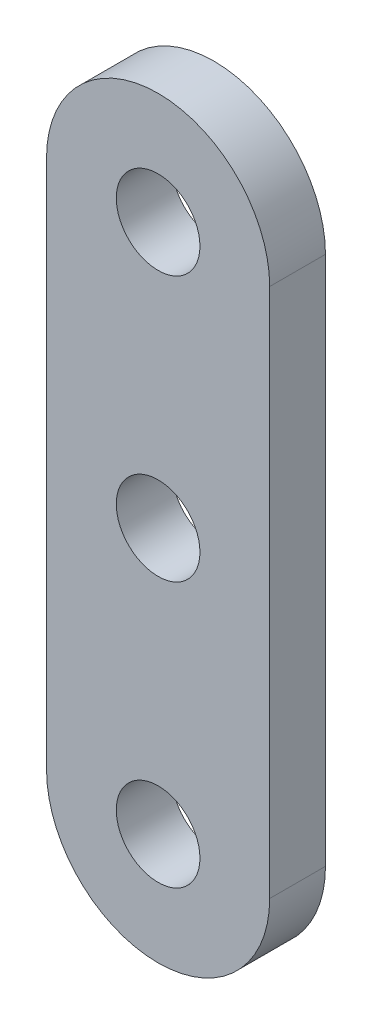
SolidWorks part; units mm, degrees
ref_plane "Front Plane" through (0, 0, 0) normal (0, 0, 1) x (1, 0, 0)
ref_plane "Top Plane" through (0, 0, 0) normal (0, 1, 0) x (1, 0, 0)
ref_plane "Right Plane" through (0, 0, 0) normal (1, 0, 0) x (0, 0, -1)
sketch "Sketch1" plane through (0, 0, 0) normal (0, 0, 1) x (1, 0, 0)
  line L0 (0, 27.7812) -> (0, 2.3813)
  line L1 (0, 0) -> (0, 30.1625) construction
  line L2 (-6.35, 0) -> (-6.35, 30.1625)
  line L3 (6.35, 0) -> (6.35, 30.1625)
  circle A0 centre (0, 0) radius 2.3813
  circle A1 centre (0, 30.1625) radius 2.3813
  arc A2 (-6.35, 0) -> (6.35, 0) centre (0, 0) ccw
  arc A3 (6.35, 30.1625) -> (-6.35, 30.1625) centre (0, 30.1625) ccw
  point P7 (0, 15.0813)
  dimension "D1" = 4.7625
  dimension "D2" = 4.7625
  dimension "D4" = 6.35
  dimension "D3" = 25.4
extrude "Boss-Extrude1" add sketch "Sketch1" along normal blind 3.175
sketch "Sketch2" plane through (0, 0, 3.175) normal (0, 0, 1) x (1, 0, 0)
  line L0 (0, 2.3813) -> (0, 15.0812)
  circle A0 centre (0, 15.0812) radius 2.3812
  circle A1 centre (0, 0) radius 2.3813 construction
  dimension "D1" = 4.7625
  dimension "D2" = 12.7
extrude "Cut-Extrude1" cut sketch "Sketch2" against normal blind 3.175
